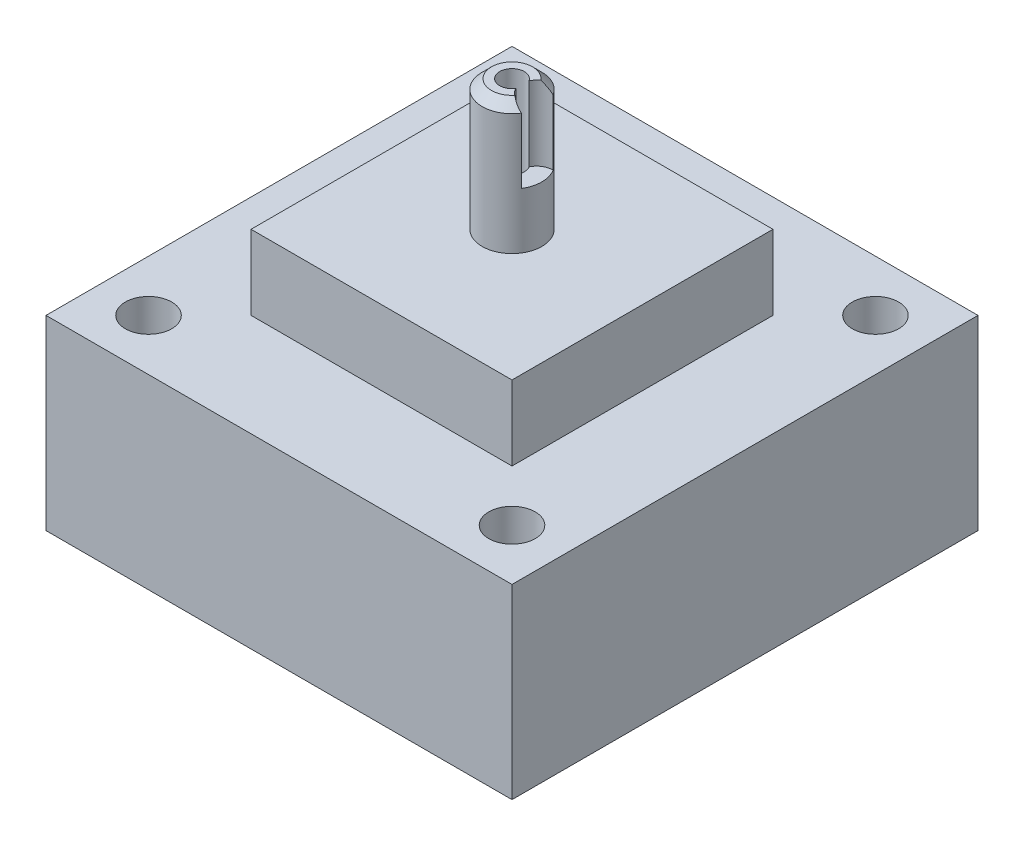
SolidWorks part; units mm, degrees
other "Markup2"
sketch "Sketch7" plane through (-12.5, 11, 12.5) normal (-0.3501, 0.7717, 0.531) x (0.0642, -0.5457, 0.8355)
other "DetailItem2"
material "6061-T6 (SS)"
ref_plane "Front Plane" through (0, 0, 0) normal (0, 0, 1) x (1, 0, 0)
ref_plane "Top Plane" through (0, 0, 0) normal (0, 1, 0) x (1, 0, 0)
ref_plane "Right Plane" through (0, 0, 0) normal (1, 0, 0) x (0, 0, -1)
sketch "Sketch1" plane through (0, 0, 0) normal (0, 1, 0) x (1, 0, 0)
  line L0 (-7, -7) -> (7, -7)
  line L1 (-7, -7) -> (-7, 7)
  line L2 (7, -7) -> (7, 7)
  line L3 (-7, 7) -> (7, 7)
  line L4 (-7, -7) -> (7, 7) construction
  line L5 (7, -7) -> (-7, 7) construction
  point P1 (0, 0)
  dimension "D1" = 14
extrude "Boss-Extrude1" add sketch "Sketch1" along normal blind 4
sketch "Sketch2" plane through (0, 0, 0) normal (0, -1, 0) x (1, 0, 0)
  line L0 (-12.5, -12.5) -> (-12.5, 12.5)
  line L1 (-12.5, -12.5) -> (12.5, -12.5)
  line L2 (-12.5, 12.5) -> (12.5, 12.5)
  line L3 (12.5, -12.5) -> (12.5, 12.5)
  line L4 (-12.5, -12.5) -> (12.5, 12.5) construction
  line L5 (-12.5, 12.5) -> (12.5, -12.5) construction
  line L6 (-0.1744, 7) -> (-0.1744, 12.5) construction
  line L7 (-7, 7) -> (7, 7) construction
  circle A0 centre (-9.75, 9.75) radius 1.2446
  circle A1 centre (9.75, 9.75) radius 1.2446
  circle A2 centre (9.75, -9.75) radius 1.2446
  circle A3 centre (-9.75, -9.75) radius 1.2446
  point P1 (0, 0)
  point P13 (-0.1744, 9.75)
  point P17 (0, 0)
  point P20 (0, 0)
  point P23 (0, 0)
  point P25 (0, 0)
  dimension "D2" = 2.4892
  dimension "D1" = 25
  dimension "D3" = 4
extrude "Boss-Extrude2" add sketch "Sketch2" along normal blind 10
sketch "Sketch3" plane through (0, -10, 0) normal (0, -1, 0) x (1, 0, 0)
  line L0 (-12.5, 12.5) -> (12.5, -12.5) construction
  circle A0 centre (0, 0) radius 4.23
  dimension "D1" = 8.46
extrude "Cut-Extrude1" cut sketch "Sketch3" against normal blind 9.8
sketch "Sketch4" plane through (0, 0, 0) normal (1, 0, 0) x (0, 0, -1)
  line L0 (0, 4) -> (0, 6.6565) construction
  line L1 (-7, 4) -> (7, 4) construction
  line L2 (0.6604, 11) -> (0.6604, 4)
  line L3 (0.6604, 4) -> (1.6, 4)
  line L4 (1.6, 4) -> (1.6, 10.5)
  line L5 (1.6, 10.5) -> (1.1, 11)
  line L6 (1.1, 11) -> (0.6604, 11)
  dimension "D1" = 7
  dimension "D2" = 1.6
  dimension "D3" = 45
  dimension "D4" = 0.5
  dimension "D5" = 0.6604
revolve "Revolve1" add sketch "Sketch4" angle 360 about L0
sketch "Sketch5" plane through (0, 4, 0) normal (0, 1, 0) x (1, 0, 0)
  circle A0 centre (0, 0) radius 0.6604
extrude "Cut-Extrude2" cut sketch "Sketch5" against normal up to surface (14 mm away) up to face at (0, -10, -4.23)
sketch "Sketch8" plane through (0, 11, 0) normal (0, 1, 0) x (1, 0, 0)
  line L0 (0, 0) -> (1.3346, 0) construction
  line L1 (0.56, 0.35) -> (3.3409, 0.35)
  line L2 (0.56, -0.35) -> (3.3409, -0.35)
  circle A0 centre (1.3346, 0) radius 0.85
  circle A1 centre (0, 0) radius 0.6604 construction
  dimension "D1" = 1.7
  dimension "D2" = 0.7
extrude "Cut-Extrude3" cut sketch "Sketch8" against normal blind 4 contours A0
